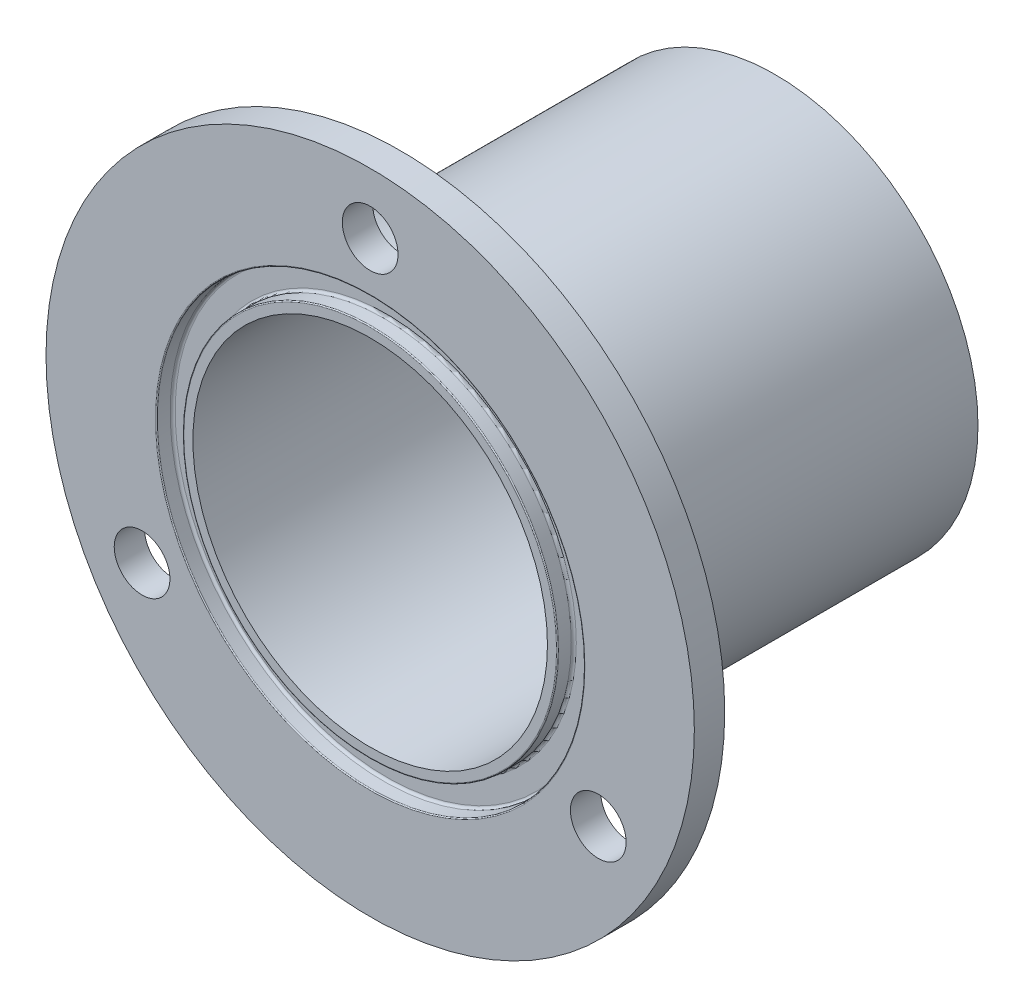
SolidWorks part; units mm, degrees
ref_plane "Front Plane" through (0, 0, 0) normal (0, 0, 1) x (1, 0, 0)
ref_plane "Top Plane" through (0, 0, 0) normal (0, 1, 0) x (1, 0, 0)
ref_plane "Right Plane" through (0, 0, 0) normal (1, 0, 0) x (0, 0, -1)
sketch "Sketch1" plane through (0, 0, 0) normal (0, 0, 1) x (1, 0, 0)
  circle A0 centre (0, 0) radius 20
  circle A1 centre (0, 0) radius 17.5
  dimension "D1" = 40
  dimension "D2" = 2.5
extrude "Boss-Extrude1" add sketch "Sketch1" along normal mid plane 40
sketch "Sketch2" plane through (0, 0, 20) normal (0, 0, 1) x (1, 0, 0)
  circle A2 centre (0, 0) radius 32
  circle A3 centre (0, 0) radius 32
  circle A5 centre (0, 0) radius 20 construction
  circle A6 centre (0, 0) radius 20
  dimension "D1" = 12
extrude "Boss-Extrude2" add sketch "Sketch2" against normal blind 3 separate body
hole_wizard "M5 Clearance Hole1" positions "Sketch3" profile "Sketch4" hole size "M5" standard "ISO" end condition through all
sketch "Sketch3" plane through (0, 0, 17) normal (0, 0, -1) x (-1, 0, 0)
  line L0 (0, 0) -> (0, 26) construction
  line L1 (0, 32) -> (0, 20) construction
  circle A4 centre (0, 0) radius 26
  circle A8 centre (0, 0) radius 20 construction
  circle A9 centre (0, 0) radius 32 construction
  point P0 (0, 26)
  point P30 (0, 0)
  point P31 (0, 0)
  dimension "D1" = 52
sketch "Sketch4" plane through (0, 26, 17) normal (1, 0, 0) x (0, 1, 0)
  line L0 (0, 0) -> (0, 3)
  line L1 (0, 3) -> (2.75, 3)
  line L2 (2.75, 3) -> (2.75, 0)
  line L5 (2.75, 0) -> (0, 0)
  line L11 (0, -6.35) -> (0, 107.95) construction
  dimension "Thru Hole Dia." = 5.5
  dimension "Thru Hole Depth" = 3
pattern_circular "CirPattern1" count 3 over 360 about axis through (0, 0, 0) along (0, 0, 1) of "M5 Clearance Hole1"
chamfer "Chamfer1" distance 1 angle 45 1 edges at (17.5, 0, -20)
combine bodies "Combine1" operation type add bodies to combine 101 104
sketch "Sketch5" plane through (0, 0, 20) normal (0, 0, 1) x (1, 0, 0)
  circle A0 centre (0, 0) radius 18.5
  circle A1 centre (0, 0) radius 21.1
  dimension "D1" = 37
  dimension "D2" = 2.6
extrude "Cut-Extrude1" cut sketch "Sketch5" against normal blind 1.6
fillet "Fillet1" radius 0.25 2 edges at (18.5, 0, 18.4) (21.1, 0, 18.4)
fillet "Fillet2" radius 0.1 2 edges at (18.5, 0, 20) (21.1, 0, 20)
fillet "Fillet3" radius 1 1 edges at (20, 0, 17)
